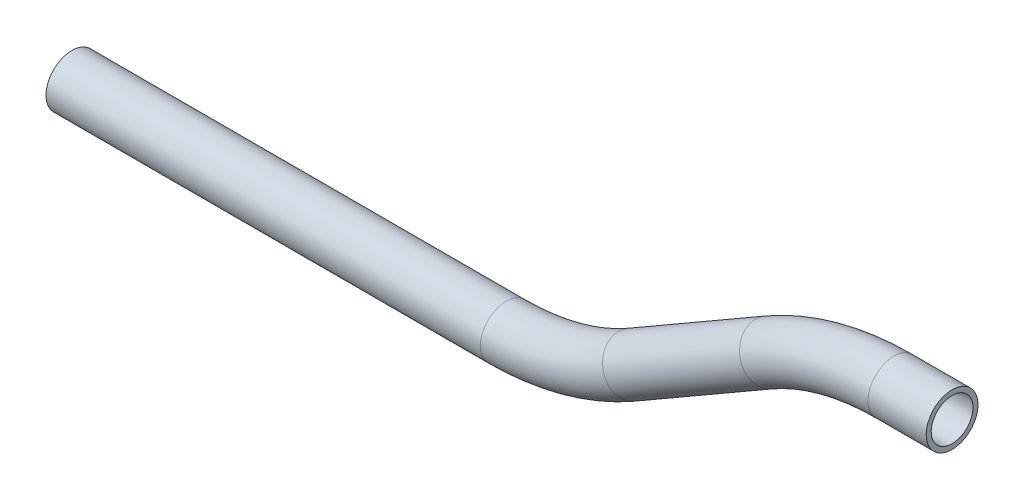
SolidWorks part; units mm, degrees
material "6061 Alloy"
ref_plane "Front Plane" through (0, 0, 0) normal (0, 0, 1) x (1, 0, 0)
ref_plane "Top Plane" through (0, 0, 0) normal (0, 1, 0) x (1, 0, 0)
ref_plane "Right Plane" through (0, 0, 0) normal (1, 0, 0) x (0, 0, -1)
sketch "Sketch4" plane through (0, 0, 0) normal (0, 0, 1) x (1, 0, 0)
  line L0 (27.5339, 15.1508) -> (45.2162, 15.1508)
  line L2 (-10.5661, 4.9419) -> (-52.1912, -19.0903)
  line L3 (-52.1912, -19.0903) -> (7.1162, 15.1508)
  line L4 (45.2162, 15.1508) -> (7.1162, 15.1508)
  line L5 (-90.2912, -29.2992) -> (-222.2735, -29.2992)
  line L6 (-222.2735, -29.2992) -> (-69.8735, -29.2992)
  line L7 (-10.5661, 4.9419) -> (-69.8735, -29.2992)
  arc A0 (27.5339, 15.1508) -> (-10.5661, 4.9419) centre (27.5339, -61.0492) ccw
  arc A1 (-52.1912, -19.0903) -> (-90.2912, -29.2992) centre (-90.2912, 46.9008) cw
  point P9 (7.1162, 15.1508)
  point P14 (-69.8735, -29.2992)
  dimension "D3" = 30
  dimension "D4" = 30
  dimension "D1" = 76.2
  dimension "D2" = 76.2
  dimension "D5" = 88.9
  dimension "D6" = 38.1
  dimension "D7" = 152.4
ref_plane "Plane2" through (45.2162, 15.1508, 0) normal (-1, 0, 0) x (0, 0, 1)
sketch "Sketch5" plane through (45.2162, 15.1508, 0) normal (-1, 0, 0) x (0, 0, 1)
  circle A0 centre (0, 0) radius 6.35
  circle A1 centre (0, 0) radius 7.874
  dimension "D1" = 15.748
  dimension "D2" = 12.7
sweep "Sweep1" add profiles "Sketch5" path "Sketch4"
sketch "Sketch6" plane through (-222.2735, 0, 0) normal (-1, 0, 0) x (0, 0, 1)
  line L0 (-7.874, -29.2992) -> (7.874, -29.2992) construction
sketch "Sketch7" plane through (0, 0, 0) normal (0, 0, 1) x (1, 0, 0)
  line L0 (-222.2735, -29.2992) -> (-136.2487, -29.2992) construction
  line L1 (-222.2735, -19.7742) -> (-222.2735, -38.8242) construction
